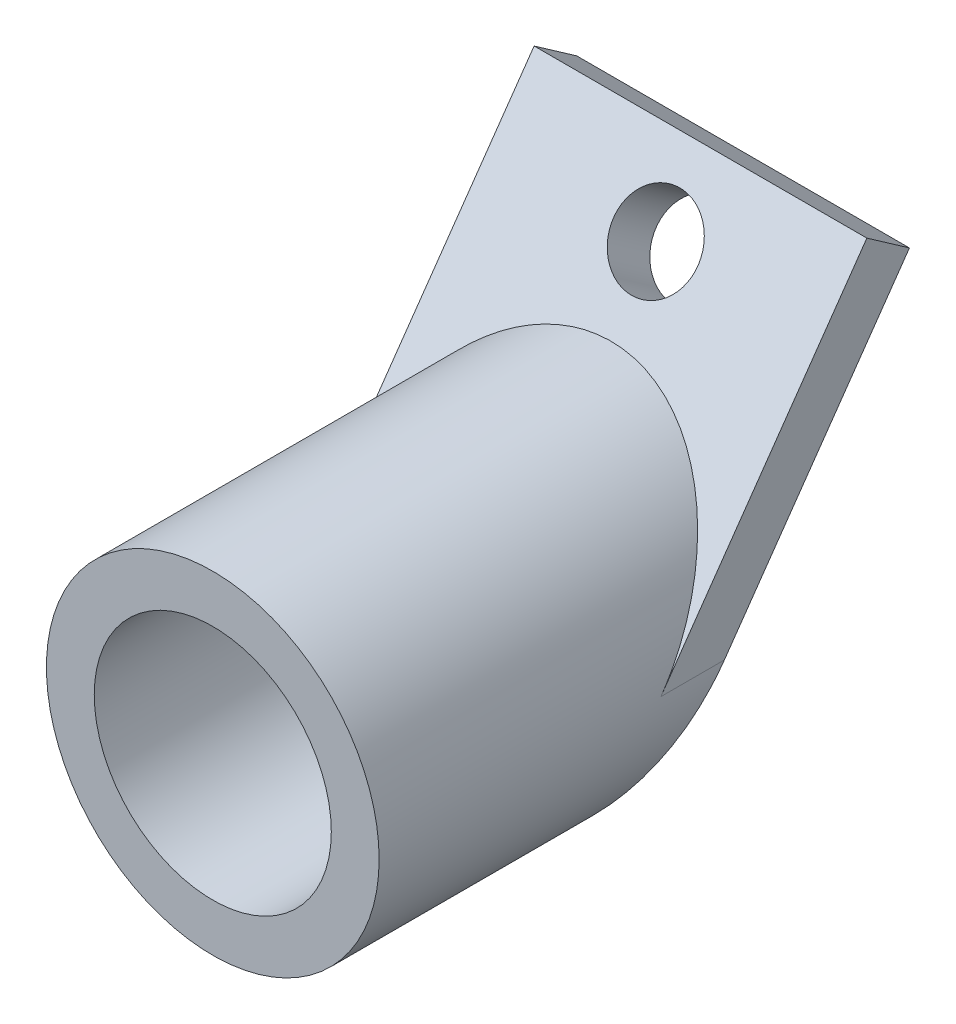
SolidWorks part; units mm, degrees
ref_plane "Front Plane" through (0, 0, 0) normal (0, 0, 1) x (1, 0, 0)
ref_plane "Top Plane" through (0, 0, 0) normal (0, 1, 0) x (1, 0, 0)
ref_plane "Right Plane" through (0, 0, 0) normal (1, 0, 0) x (0, 0, -1)
sketch "Sketch1" plane through (0, 0, 0) normal (0, 0, 1) x (1, 0, 0)
  circle A0 centre (0, 0) radius 11.4
  circle A1 centre (0, 0) radius 16
extrude "Boss-Extrude1" add sketch "Sketch1" along normal blind 20
sketch "Sketch2" plane through (0, 0, 0) normal (0, 0, -1) x (-1, 0, 0)
  circle A0 centre (0, 0) radius 16
extrude "Boss-Extrude2" add sketch "Sketch2" along normal blind 2
sketch "Sketch3" plane through (0, 0, 0) normal (1, 0, 0) x (0, 0, -1)
  line L5 (31.0022, 25.4194) -> (26.9064, 28.2873)
  line L7 (2, -16) -> (2, 16) construction
  line L8 (2, -7.2828) -> (2, -16)
  line L9 (18.3028, 16) -> (2, -7.2828)
  line L10 (18.3028, 16) -> (26.9064, 28.2873)
  line L11 (31.0022, 25.4194) -> (2, -16)
extrude "Boss-Extrude3" add sketch "Sketch3" along normal through all and the other way through all
sketch "Sketch4" plane through (0, 0, -2) normal (0, 0, -1) x (-1, 0, 0)
  line L0 (16, 0) -> (34.2665, 0)
  line L1 (34.2665, 0) -> (32.1798, -27.298)
  line L2 (32.1798, -27.298) -> (-36.4631, -20.4887)
  line L3 (-36.4631, -20.4887) -> (-34.4306, 0)
  line L4 (-34.4306, 0) -> (-16, 0)
  circle A0 centre (0, 0) radius 16
  arc M11 (14.2464, -7.2828) -> (-14.2464, -7.2828) centre (0, 0) ccw
extrude "Cut-Extrude1" cut sketch "Sketch4" along normal through all contours A0 L4 L3 L2 L1 L0 M11
sketch "Sketch5" plane through (0, 0, -2) normal (0, 0, -1) x (-1, 0, 0)
  circle A0 centre (0, 0) radius 16
extrude "Boss-Extrude4" add sketch "Sketch5" along normal up to next
sketch "Sketch6" plane through (0, -3.3356, -4.7638) normal (0, 0.5736, 0.8192) x (1, 0, 0)
  line L0 (0, 38.6045) -> (0, 23.6045) construction
  line L1 (16, 38.6045) -> (-16, 38.6045) construction
  circle A0 centre (0, 31.1045) radius 4.05
  ellipse E0 centre (0, 4.0721) end of major axis (0, 23.6045) minor radius 16 (16, 4.0721) -> (-16, 4.0721) ccw construction
extrude "Cut-Extrude3" cut sketch "Sketch6" against normal through all
